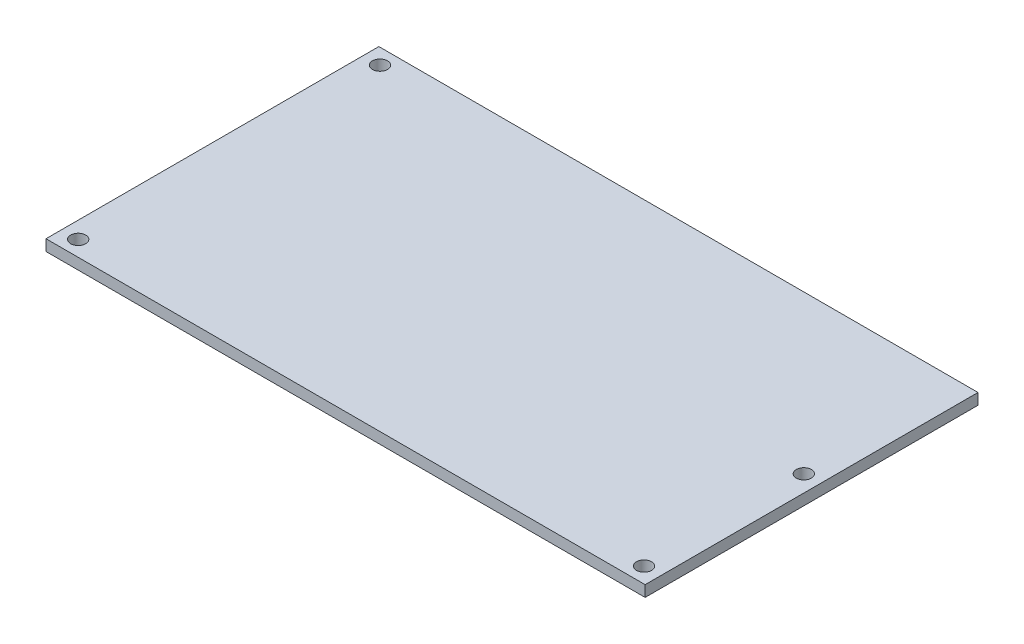
SolidWorks part; units mm, degrees
ref_plane "Front Plane" through (0, 0, 0) normal (0, 0, 1) x (1, 0, 0)
ref_plane "Top Plane" through (0, 0, 0) normal (0, 1, 0) x (1, 0, 0)
ref_plane "Right Plane" through (0, 0, 0) normal (1, 0, 0) x (0, 0, -1)
sketch "Sketch1" plane through (0, 0, 0) normal (0, 1, 0) x (1, 0, 0)
  line L1 (-67.5, 37.5) -> (67.5, 37.5)
  line L2 (-67.5, 37.5) -> (-67.5, -37.5)
  line L3 (-67.5, -37.5) -> (67.5, -37.5)
  line L4 (67.5, 37.5) -> (67.5, -37.5)
  line L5 (-67.5, 37.5) -> (67.5, -37.5) construction
  line L6 (-67.5, -37.5) -> (67.5, 37.5) construction
  point P0 (0, 0)
  dimension "D1" = 75
  dimension "D2" = 135
sketch "Sketch2" plane through (0, 0, 0) normal (0, 1, 0) x (1, 0, 0)
  line L0 (0, 37.5) -> (0, -37.5) construction
  line L1 (-67.5, 37.5) -> (67.5, 37.5) construction
  line L2 (-67.5, -37.5) -> (67.5, -37.5) construction
  line L4 (-67.5, 0) -> (67.5, 0) construction
  line L5 (-67.5, 37.5) -> (-67.5, -37.5) construction
  line L6 (67.5, 37.5) -> (67.5, -37.5) construction
  circle A0 centre (63.75, -34) radius 1.7
  circle A1 centre (63.75, 2) radius 1.7
  circle A2 centre (-63.75, -34) radius 1.7
  circle A3 centre (-63.75, 34) radius 1.7
  dimension "D1" = 3.5
  dimension "D2" = 3.4
  dimension "D4" = 36
  dimension "D3" = 127.5
extrude "Boss-Extrude1" add sketch "Sketch1" along normal blind 2.5
extrude "Cut-Extrude1" cut sketch "Sketch2" along normal up to next
